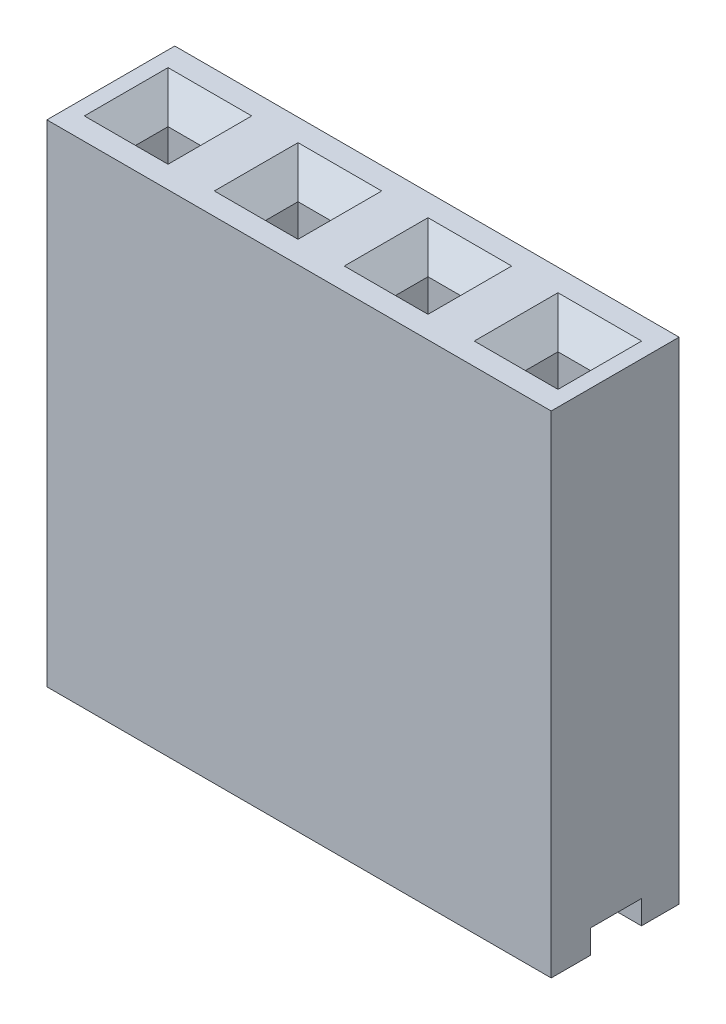
SolidWorks part; units mm, degrees
ref_plane "Alzado" through (0, 0, 0) normal (0, 0, 1) x (1, 0, 0)
ref_plane "Planta" through (0, 0, 0) normal (0, 1, 0) x (1, 0, 0)
ref_plane "Vista lateral" through (0, 0, 0) normal (1, 0, 0) x (0, 0, -1)
sketch "Croquis1" plane through (0, 0, 0) normal (0, 1, 0) x (1, 0, 0)
  line L0 (0, 0) -> (0, -2.5)
  line L1 (0, 0) -> (9.859, 0)
  line L3 (9.859, -2.5) -> (0, -2.5)
  line L4 (0, -2.5) -> (0.8, -2.5) construction
  line L5 (0.8, -2.5) -> (0.8, 0) construction
  line L6 (1.436, -1.25) -> (3.341, -1.25) construction
  line L7 (0.8, 0) -> (1.436, 0) construction
  line L8 (1.436, 0) -> (1.436, -2.5) construction
  line L9 (0.8, -1.25) -> (0.8, -0.932) construction
  line L10 (2.3885, 0) -> (2.3885, -2.5) construction
  line L11 (0.8, -0.932) -> (1.436, -0.932)
  line L12 (0.8, -0.932) -> (0.8, -1.568)
  line L13 (0.8, -1.568) -> (1.436, -1.568)
  line L14 (1.436, -0.932) -> (1.436, -1.568)
  line L15 (3.341, -0.932) -> (3.341, -1.568)
  line L16 (3.977, -1.568) -> (3.341, -1.568)
  line L17 (3.977, -0.932) -> (3.977, -1.568)
  line L18 (3.977, -0.932) -> (3.341, -0.932)
  line L19 (0, -1.25) -> (0.8, -1.25) construction
  line L20 (3.977, -1.25) -> (5.882, -1.25) construction
  line L21 (4.9295, 0) -> (4.9295, -2.5) construction
  line L22 (9.059, -0.932) -> (9.059, -1.568)
  line L23 (8.423, -0.932) -> (8.423, -1.568)
  line L24 (9.059, -0.932) -> (8.423, -0.932)
  line L25 (9.059, -1.568) -> (8.423, -1.568)
  line L26 (5.882, -0.932) -> (5.882, -1.568)
  line L27 (6.518, -0.932) -> (6.518, -1.568)
  line L28 (5.882, -1.568) -> (6.518, -1.568)
  line L29 (5.882, -0.932) -> (6.518, -0.932)
  line L30 (9.059, -1.25) -> (9.859, -1.25) construction
  line L31 (9.859, 0) -> (9.859, -2.5)
  dimension "D1" = 0.636
  dimension "D2" = 0.636
extrude "Saliente-Extruir2" add sketch "Croquis1" along normal blind 9.6
chamfer "Chaflán2" distance 0.5 angle 45 4 edges at (1.118, 9.6, 1.568) (1.436, 9.6, 1.25) (1.118, 9.6, 0.932) (0.8, 9.6, 1.25)
chamfer "Chaflán3" distance 0.5 angle 45 12 edges at (8.741, 9.6, 1.568) (9.059, 9.6, 1.25) (8.741, 9.6, 0.932) (8.423, 9.6, 1.25) (6.2, 9.6, 1.568) (6.518, 9.6, 1.25) (6.2, 9.6, 0.932) (5.882, 9.6, 1.25) (3.659, 9.6, 1.568) (3.977, 9.6, 1.25) (3.659, 9.6, 0.932) (3.341, 9.6, 1.25)
sketch "Croquis2" plane through (0, 0, 0) normal (-1, 0, 0) x (0, 0, 1)
  line L0 (0, 0) -> (0.7356, 0) construction
  line L1 (0, 0) -> (2.5, 0) construction
  line L2 (2.5, 0) -> (1.7366, 0) construction
  line L4 (0.7356, 0) -> (1.7366, 0)
  line L5 (0.7356, 0) -> (0.7356, 0.4632)
  line L6 (0.7356, 0.4632) -> (1.7366, 0.4632)
  line L7 (1.7366, 0) -> (1.7366, 0.4632)
extrude "Cortar-Extruir1" cut sketch "Croquis2" against normal through all
